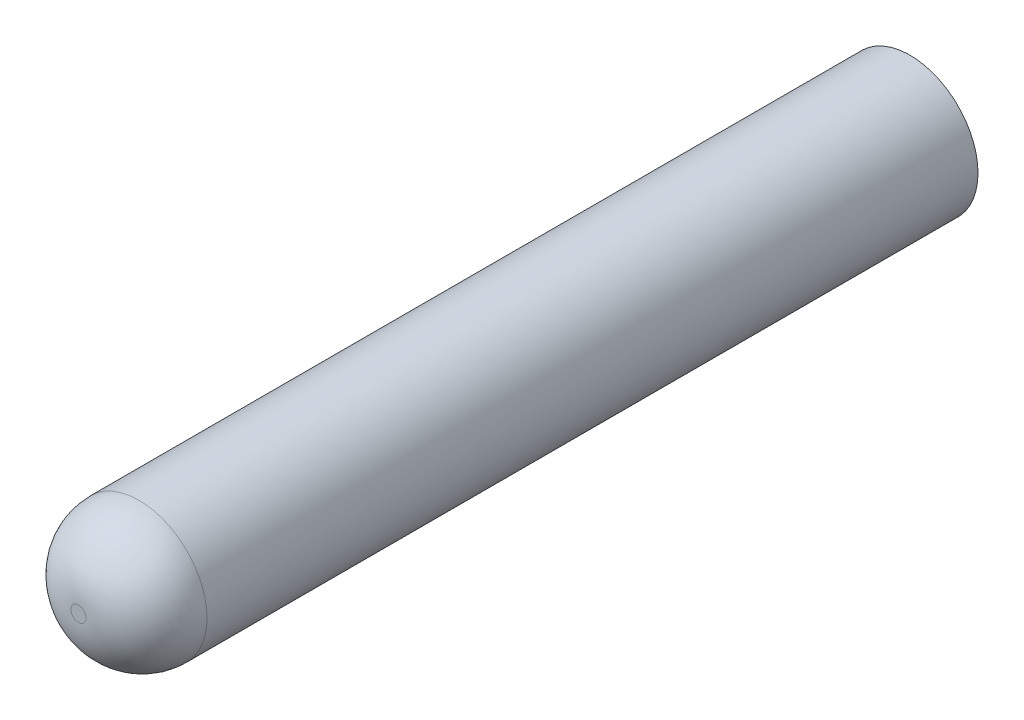
SolidWorks part; units mm, degrees
ref_plane "Front Plane" through (0, 0, 0) normal (0, 0, 1) x (1, 0, 0)
ref_plane "Top Plane" through (0, 0, 0) normal (0, 1, 0) x (1, 0, 0)
ref_plane "Right Plane" through (0, 0, 0) normal (1, 0, 0) x (0, 0, -1)
sketch "草图1" plane through (0, 0, 0) normal (0, 0, 1) x (1, 0, 0)
  circle A0 centre (0, 0) radius 2.25
  dimension "D1" = 4.5
extrude "凸台-拉伸2" add sketch "草图1" along normal blind 27.5
sketch "草图7" plane through (0, 0, 0) normal (0, 0, 1) x (1, 0, 0)
  line L1 (1.2, -1.2) -> (-1.2, -1.2)
  line L2 (1.2, -1.2) -> (1.2, 1.2)
  line L3 (1.2, 1.2) -> (-1.2, 1.2)
  line L4 (-1.2, -1.2) -> (-1.2, 1.2)
  line L5 (1.2, -1.2) -> (-1.2, 1.2) construction
  line L6 (1.2, 1.2) -> (-1.2, -1.2) construction
  point P0 (0, 0)
  dimension "D1" = 2.4
  dimension "D2" = 2.4
extrude "切除-拉伸3" cut sketch "草图7" along normal blind 4.5 from surface at 0 starting at face at (2.25, 0, 0)
fillet "圆角2" radius 2 1 edges at (2.25, 0, 27.5)
